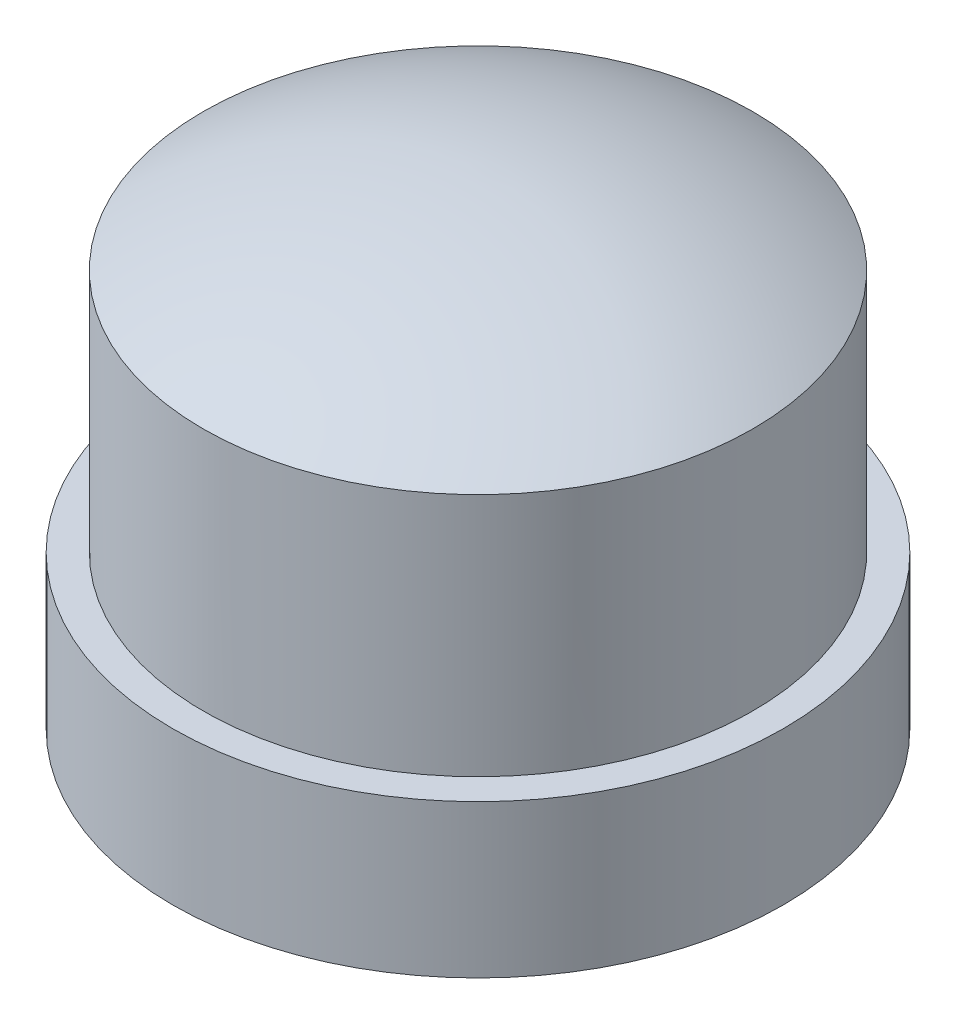
SolidWorks part; units mm, degrees
ref_plane "Front" through (0, 0, 0) normal (0, 0, 1) x (1, 0, 0)
ref_plane "Top" through (0, 0, 0) normal (0, 1, 0) x (1, 0, 0)
ref_plane "Right" through (0, 0, 0) normal (1, 0, 0) x (0, 0, -1)
sketch "Sketch1" plane through (0, 0, 0) normal (0, 1, 0) x (1, 0, 0)
  circle A0 centre (0, 0) radius 10
  dimension "D1" = 20
extrude "Boss-Extrude1" add sketch "Sketch1" along normal blind 5
sketch "Sketch2" plane through (0, 0, 0) normal (1, 0, 0) x (0, 0, -1)
  line L0 (0, 5) -> (0, 15.5) construction
  line L1 (10, 5) -> (-10, 5) construction
  line L2 (0, 15.5) -> (-9, 15.5) construction
  line L3 (-9, 15.5) -> (-9, 5) construction
  line L4 (-9, 5) -> (0, 5) construction
  line L5 (-9, 13) -> (-9, 5)
  line L6 (-9, 5) -> (0, 5)
  line L7 (0, 5) -> (0, 15.5)
  arc A0 (-9, 13) -> (0, 15.5) centre (0, -1.95) cw
  dimension "D2" = 8
  dimension "D1" = 9
  dimension "D3" = 2.5
revolve "Revolve1" add sketch "Sketch2" angle 360 about L7
